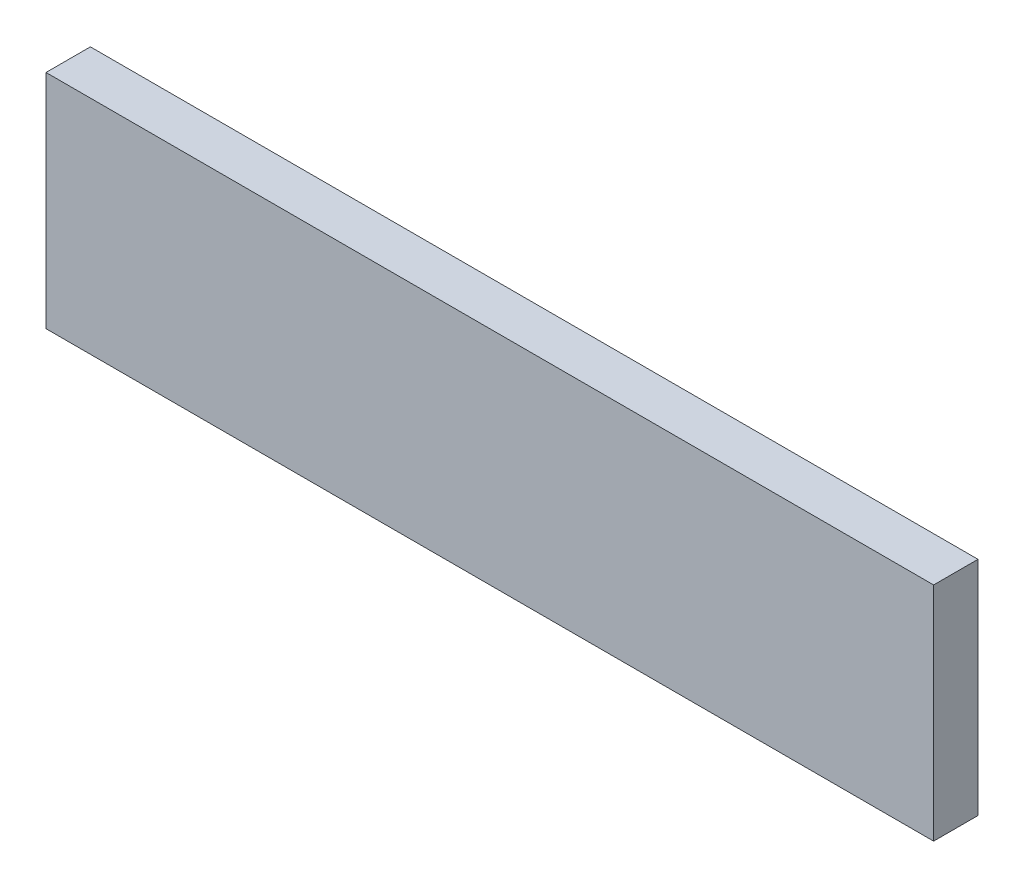
SolidWorks part; units mm, degrees
ref_plane "Спереди" through (0, 0, 0) normal (0, 0, 1) x (1, 0, 0)
ref_plane "Сверху" through (0, 0, 0) normal (0, 1, 0) x (1, 0, 0)
ref_plane "Справа" through (0, 0, 0) normal (1, 0, 0) x (0, 0, -1)
sketch "Эскиз1" plane through (0, 0, 0) normal (1, 0, 0) x (0, 0, -1)
  line L1 (0, 0) -> (10, 0)
  line L2 (0, 0) -> (0, 50)
  line L3 (0, 50) -> (10, 50)
  line L4 (10, 0) -> (10, 50)
extrude "Бобышка-Вытянуть1" add sketch "Эскиз1" along normal blind 200
